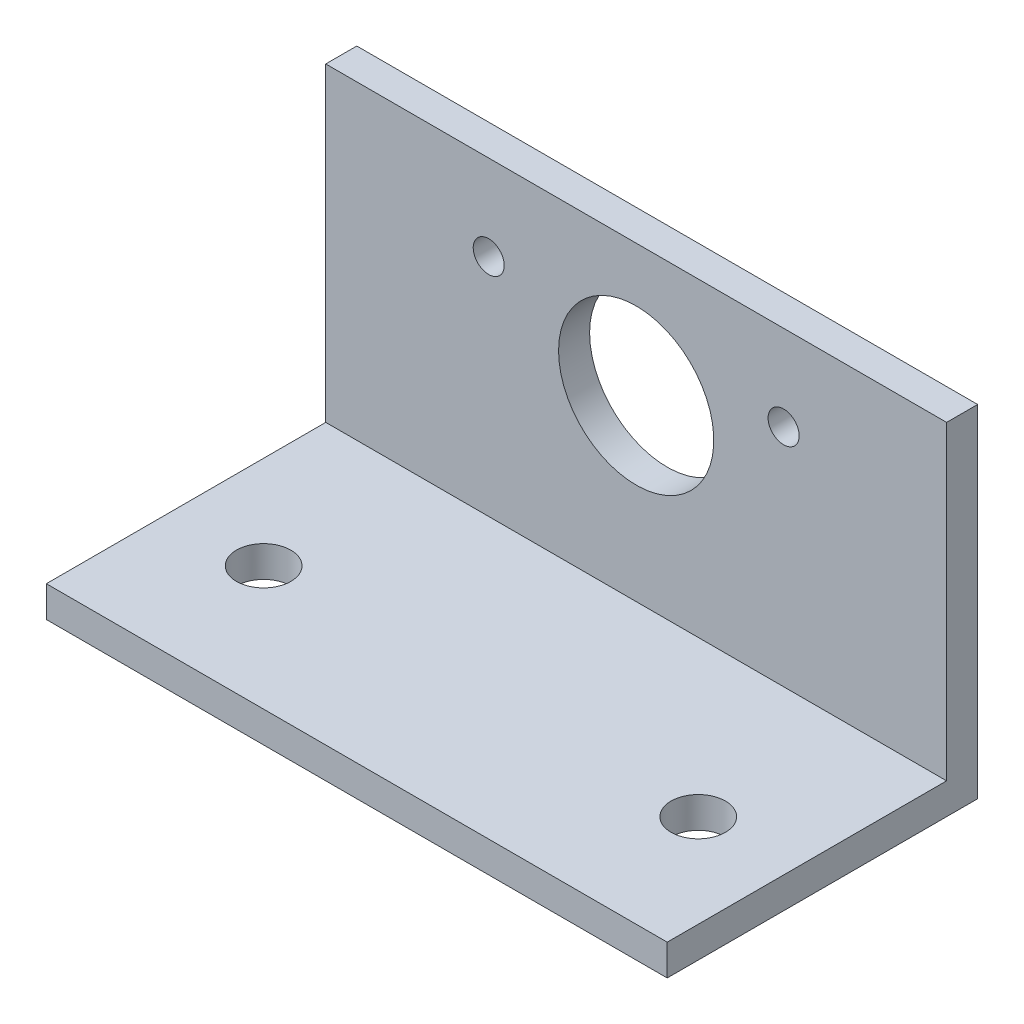
SolidWorks part; units mm, degrees
ref_plane "Front Plane" through (0, 0, 0) normal (0, 0, 1) x (1, 0, 0)
ref_plane "Top Plane" through (0, 0, 0) normal (0, 1, 0) x (1, 0, 0)
ref_plane "Right Plane" through (0, 0, 0) normal (1, 0, 0) x (0, 0, -1)
sketch "Sketch1" plane through (0, 0, 0) normal (0, 1, 0) x (1, 0, 0)
  line L1 (-20, 10) -> (20, 10)
  line L2 (-20, 10) -> (-20, -10)
  line L3 (-20, -10) -> (20, -10)
  line L4 (20, 10) -> (20, -10)
  line L5 (-20, 10) -> (20, -10) construction
  line L6 (-20, -10) -> (20, 10) construction
  point P0 (0, 0)
  dimension "D1" = 40
  dimension "D2" = 20
extrude "Boss-Extrude1" add sketch "Sketch1" along normal blind 2
sketch "Sketch2" plane through (0, 2, 0) normal (0, 1, 0) x (1, 0, 0)
  line L0 (20, -10) -> (20, 10) construction
  line L1 (-20, 10) -> (20, 10)
  line L2 (-20, 10) -> (-20, 8)
  line L3 (-20, 8) -> (20, 8)
  line L4 (20, 10) -> (20, 8)
  dimension "D1" = 2
extrude "Boss-Extrude2" add sketch "Sketch2" along normal blind 20
sketch "Sketch3" plane through (0, 0, 0) normal (0, -1, 0) x (1, 0, 0)
  line L0 (20, -10) -> (-20, -10) construction
  line L1 (-20, -10) -> (-20, 10) construction
  line L2 (20, 10) -> (20, -10) construction
  circle A0 centre (-14, 2) radius 1.75
  circle A1 centre (14, 2) radius 1.75
  dimension "D5" = 3.5
  dimension "D6" = 3.5
  dimension "D1" = 12
  dimension "D2" = 6
  dimension "D3" = 6
  dimension "D4" = 12
  dimension "D7" = 28
extrude "Cut-Extrude1" cut sketch "Sketch3" against normal through all
sketch "Sketch4" plane through (0, 0, -10) normal (0, 0, -1) x (-1, 0, 0)
  line L1 (-20, 0) -> (20, 0) construction
  circle A0 centre (0, 13.5) radius 5
  circle A1 centre (-9.5, 16.5) radius 1
  circle A2 centre (9.5, 16.5) radius 1
  dimension "D2" = 10
  dimension "D1" = 13.5
  dimension "D3" = 9.5
  dimension "D4" = 16.5
  dimension "D5" = 16.5
  dimension "D6" = 9.5
  dimension "D7" = 3
extrude "Cut-Extrude2" cut sketch "Sketch4" against normal through all
